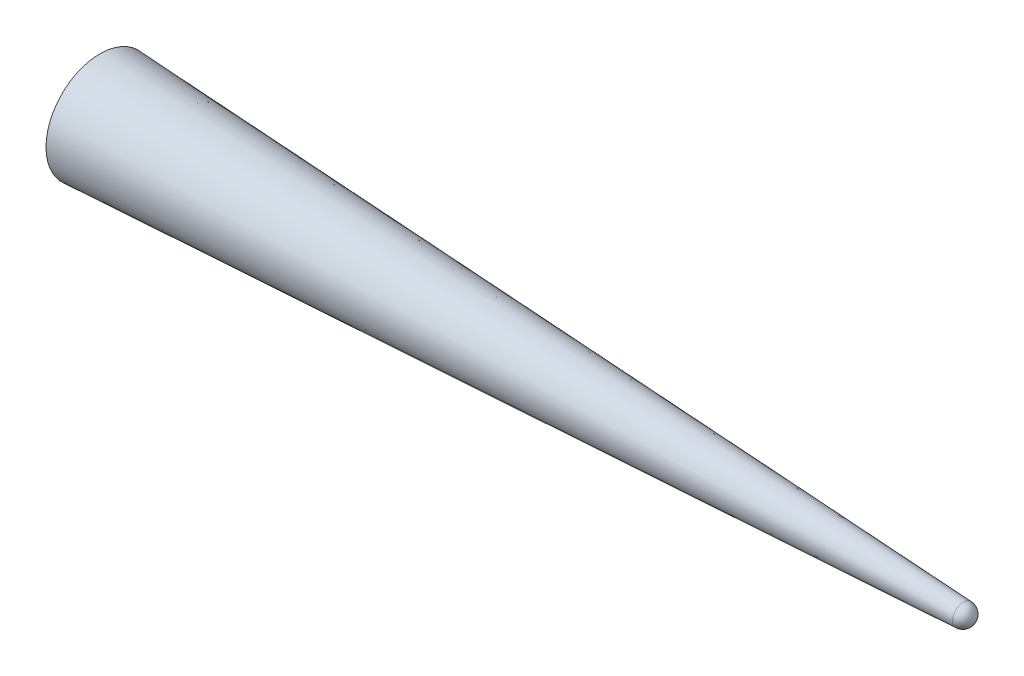
SolidWorks part; units mm, degrees
ref_plane "Front Plane" through (0, 0, 0) normal (0, 0, 1) x (1, 0, 0)
ref_plane "Top Plane" through (0, 0, 0) normal (0, 1, 0) x (1, 0, 0)
ref_plane "Right Plane" through (0, 0, 0) normal (1, 0, 0) x (0, 0, -1)
sketch "Sketch1" plane through (0, 0, 0) normal (0, 1, 0) x (1, 0, 0)
  line L2 (0, 0) -> (0, 50)
  line L9 (0, 0) -> (1000, 0) construction
  line L10 (800.2495, 9.9875) -> (0, 50)
  line L13 (0, 0) -> (809.7502, 0)
  arc A1 (809.7502, 0) -> (800.2495, 9.9875) centre (799.7502, 0) ccw
  point P10 (809.7502, 0)
  dimension "D4" = 10
  dimension "D1" = 50
  dimension "D2" = 1000
revolve "Revolve2" add sketch "Sketch1" angle 360 about L9
